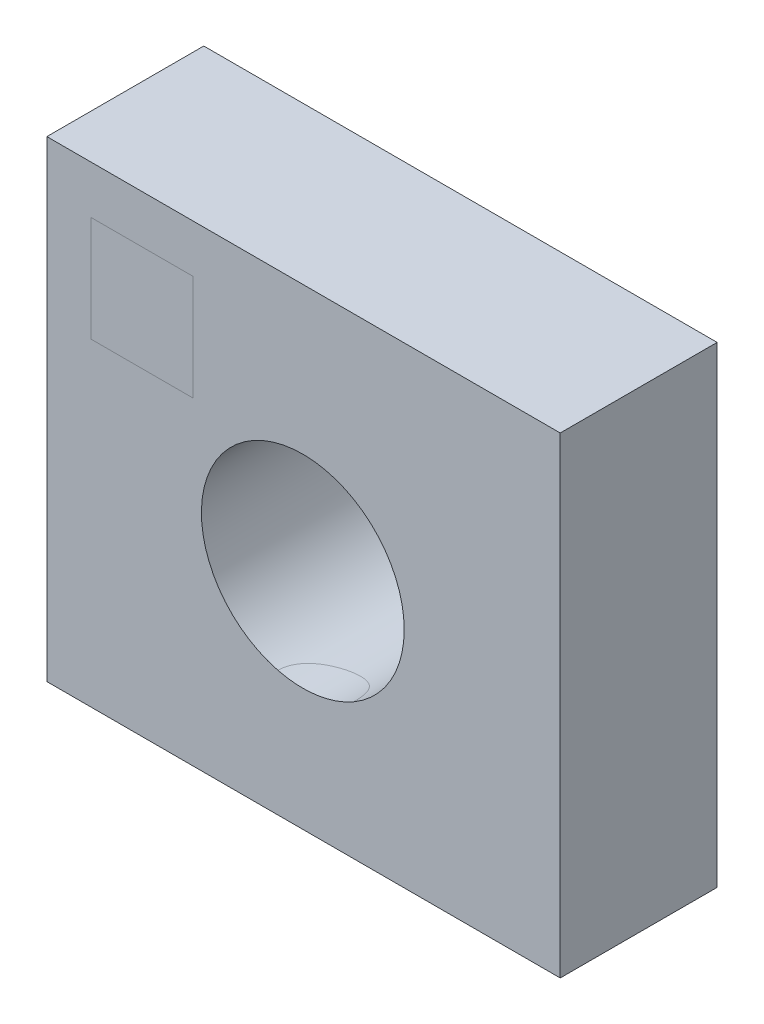
SolidWorks part; units mm, degrees
ref_plane "Ebene vorne" through (0, 0, 0) normal (0, 0, 1) x (1, 0, 0)
ref_plane "Ebene oben" through (0, 0, 0) normal (0, 1, 0) x (1, 0, 0)
ref_plane "Ebene rechts" through (0, 0, 0) normal (1, 0, 0) x (0, 0, -1)
sketch "Skizze1" plane through (0, 0, 0) normal (0, 0, 1) x (1, 0, 0)
  line L1 (0, -23.7459) -> (49.078, -23.7459)
  line L2 (0, -23.7459) -> (0, 21.3792)
  line L3 (0, 21.3792) -> (49.078, 21.3792)
  line L4 (49.078, -23.7459) -> (49.078, 21.3792)
extrude "Aufsatz-Linear austragen1" add sketch "Skizze1" along normal blind 15
sketch "Skizze2" plane through (0, 0, 15) normal (0, 0, 1) x (1, 0, 0)
  circle A0 centre (24.4687, -2.3667) radius 9.6933
extrude "Schnitt-Linear austragen1" cut sketch "Skizze2" against normal through all
sketch "Skizze3" plane through (0, 0, 15) normal (0, 0, 1) x (1, 0, 0)
  line L0 (49.078, 21.3792) -> (0, 21.3792) construction
  line L1 (4.212, 16.7949) -> (13.9489, 16.7949)
  line L2 (4.212, 16.7949) -> (4.212, 6.7187)
  line L3 (4.212, 6.7187) -> (13.9489, 6.7187)
  line L4 (13.9489, 16.7949) -> (13.9489, 6.7187)
  line L5 (0, 21.3792) -> (0, -23.7459) construction
  dimension "D1" = 4.5843
  dimension "D2" = 4.212
split line "Trennlinie1"
sketch "Skizze4" plane through (0, 0, 0) normal (0, 1, 0) x (1, 0, 0)
  line L0 (49.078, -15) -> (0, -15) construction
  circle A0 centre (25.7128, -15) radius 3.6238
split line "Trennlinie3"
